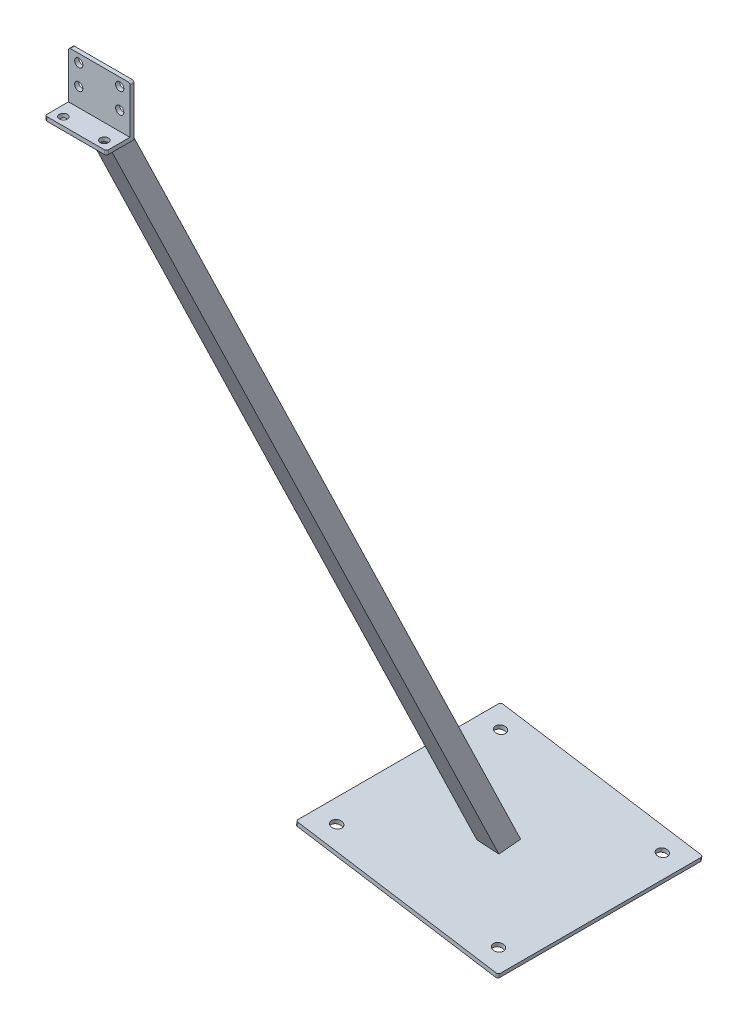
SolidWorks part; units mm, degrees
ref_plane "Front Plane" through (0, 0, 0) normal (0, 0, 1) x (1, 0, 0)
ref_plane "Top Plane" through (0, 0, 0) normal (0, 1, 0) x (1, 0, 0)
ref_plane "Right Plane" through (0, 0, 0) normal (1, 0, 0) x (0, 0, -1)
sketch "Sketch1" plane through (0, 0, 0) normal (1, 0, 0) x (0, 0, -1)
  line L0 (0, 0) -> (0, 50)
  line L1 (0, 50) -> (-4, 50)
  line L2 (-4, 50) -> (-4, 4)
  line L3 (-4, 4) -> (-27, 4)
  line L4 (-27, 4) -> (-27, 0)
  line L5 (-27, 0) -> (0, 0)
  dimension "D1" = 4
  dimension "D2" = 4
  dimension "D3" = 27
  dimension "D4" = 50
extrude "Boss-Extrude1" add sketch "Sketch1" along normal blind 60
ref_plane "Plane1" through (0, 0, 0) normal (0, -0.866, -0.5) x (-1, 0, 0)
sketch "Sketch2" plane through (0, 0, 0) normal (0, -0.866, -0.5) x (-1, 0, 0)
  line L0 (-30, 0) -> (-30, -23.3827)
  line L1 (-60, 0) -> (0, 0) construction
  line L2 (-60, -23.3827) -> (0, -23.3827) construction
ref_plane "Plane2" through (0.7342, 4.0142, 2.3176) normal (-0.1564, -0.8554, -0.4938) x (0, -0.5, 0.866)
sketch "Sketch3" plane through (0.7342, 4.0142, 2.3176) normal (-0.1564, -0.8554, -0.4938) x (0, -0.5, 0.866)
  line L0 (-9, -38.6307) -> (-9, -20.6307)
  line L1 (10, -39.6307) -> (-10, -39.6307)
  line L2 (10, -39.6307) -> (10, -19.6307)
  line L3 (10, -19.6307) -> (-10, -19.6307)
  line L4 (-10, -39.6307) -> (-10, -19.6307)
  line L5 (10, -39.6307) -> (-10, -19.6307) construction
  line L6 (10, -19.6307) -> (-10, -39.6307) construction
  line L7 (9, -20.6307) -> (-9, -20.6307)
  line L8 (9, -38.6307) -> (9, -20.6307)
  line L9 (9, -38.6307) -> (-9, -38.6307)
  point P0 (0, -29.6307)
  dimension "D1" = 20
  dimension "D2" = 20
  dimension "D3" = 1
extrude "Boss-Extrude2" add sketch "Sketch3" along normal blind 2000 and the other way blind 20
sketch "Sketch5" plane through (0, 0, 0) normal (-1, 0, 0) x (0, 0, 1)
  line L0 (4, 4) -> (4, 36.0549)
  line L1 (4, 50) -> (4, 4) construction
  line L2 (4, 36.0549) -> (38.7814, 4)
  line L3 (4, 4) -> (27, 4) construction
  line L4 (38.7814, 4) -> (4, 4)
extrude "Cut-Extrude1" cut sketch "Sketch5" against normal blind 60
ref_plane "Plane3" through (-155.5473, -982.0868, 0) normal (0.1564, 0.9877, 0) x (0.9877, -0.1564, 0)
sketch "Sketch7" plane through (-155.5473, -982.0868, 0) normal (0.1564, 0.9877, 0) x (0.9877, -0.1564, 0)
  line L0 (19.2115, 0) -> (-22.5192, 995.5664) construction
  line L1 (-22.5192, 995.5664) -> (-2.5847, 997.1308) construction
  line L3 (105.477, 466.4414) -> (-94.523, 466.4414)
  line L4 (105.477, 466.4414) -> (105.477, 666.4414)
  line L5 (105.477, 666.4414) -> (-94.523, 666.4414)
  line L6 (-94.523, 466.4414) -> (-94.523, 666.4414)
  line L7 (105.477, 466.4414) -> (-94.523, 666.4414) construction
  line L8 (105.477, 666.4414) -> (-94.523, 466.4414) construction
  point P0 (5.477, 566.4414)
  point P5 (5.477, 566.4414)
  dimension "D1" = 10
  dimension "D2" = 430
  dimension "D3" = 200
  dimension "D4" = 200
extrude "Boss-Extrude3" add sketch "Sketch7" along normal blind 4
sketch "Sketch8" plane through (-155.5473, -982.0868, 0) normal (-0.1564, -0.9877, 0) x (0.9877, -0.1564, 0)
  line L1 (-50.2657, -545.5822) -> (58.9366, -545.5822)
  line L2 (-50.2657, -545.5822) -> (-50.2657, -1028.5491)
  line L3 (-50.2657, -1028.5491) -> (58.9366, -1028.5491)
  line L4 (58.9366, -545.5822) -> (58.9366, -1028.5491)
extrude "Cut-Extrude3" cut sketch "Sketch8" along normal blind 1000
sketch "Sketch9" plane through (0, 0, 0) normal (0, 0, -1) x (-1, 0, 0)
  circle A0 centre (-50, 22) radius 4 construction
  circle A1 centre (-10, 22) radius 4 construction
  circle A2 centre (-10, 42) radius 4 construction
  circle A3 centre (-50, 42) radius 4 construction
  circle A4 centre (-50, 22) radius 4
  circle A5 centre (-10, 22) radius 4
  circle A6 centre (-10, 42) radius 4
  circle A7 centre (-50, 42) radius 4
extrude "Cut-Extrude4" cut sketch "Sketch9" against normal up to next
sketch "Sketch10" plane through (0, 0, 0) normal (0, -1, 0) x (1, 0, 0)
  circle A0 centre (50, 19) radius 4 construction
  circle A1 centre (10, 19) radius 4 construction
  circle A2 centre (50, 19) radius 4
  circle A3 centre (10, 19) radius 4
extrude "Cut-Extrude5" cut sketch "Sketch10" against normal up to next
sketch "Sketch11" plane through (-155.5473, -982.0868, 0) normal (-0.1564, -0.9877, 0) x (0.9877, -0.1564, 0)
  line L0 (-94.523, -466.4414) -> (105.477, -466.4414) construction
  line L1 (-94.523, -666.4414) -> (-94.523, -466.4414) construction
  circle A0 centre (-74.523, -486.4414) radius 5
  circle A1 centre (85.477, -486.4414) radius 5
  circle A2 centre (85.477, -646.4414) radius 5
  circle A3 centre (-74.523, -646.4414) radius 5
  dimension "D1" = 10
  dimension "D4" = 2
  dimension "D2" = 20
  dimension "D3" = 20
  dimension "D6" = 160
  dimension "D7" = 160
  dimension "D5" = 2
extrude "Cut-Extrude6" cut sketch "Sketch11" against normal up to next
fillet "Fillet1" radius 2 4 edges at (60, 2, 27) (0, 2, 27) (0, 50, 2) (60, 50, 2)
fillet "Fillet2" radius 2 4 edges at (-51.056, -996.6116, -666.4414) (-248.5936, -965.3247, -666.4414) (-51.056, -996.6116, -466.4414) (-248.5936, -965.3247, -466.4414)
